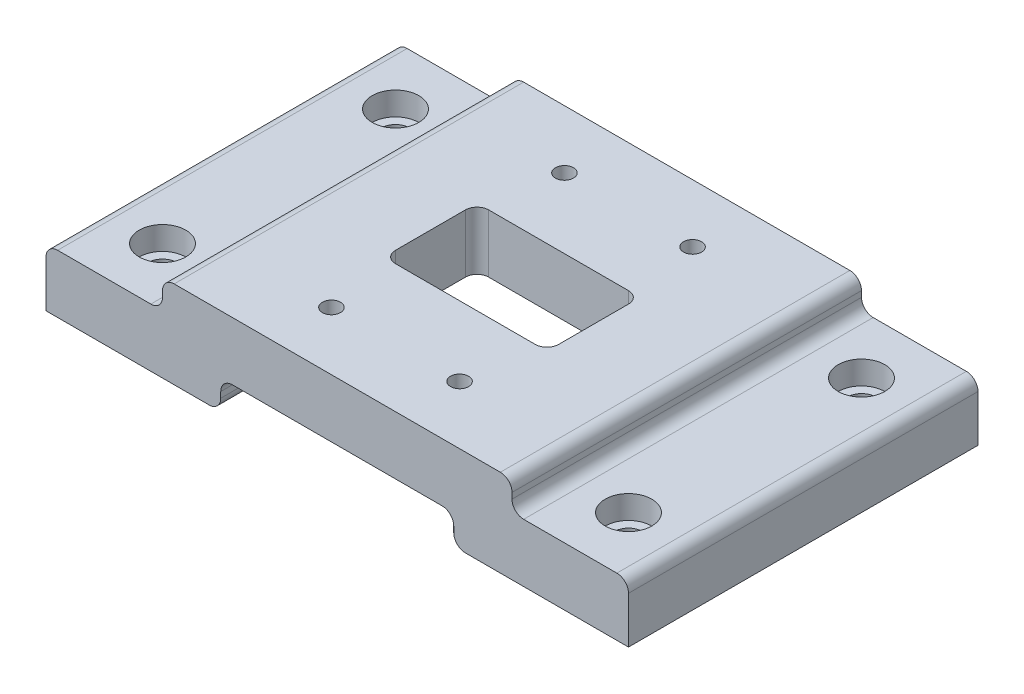
SolidWorks part; units mm, degrees
ref_plane "Front Plane" through (0, 0, 0) normal (0, 0, 1) x (1, 0, 0)
ref_plane "Top Plane" through (0, 0, 0) normal (0, 1, 0) x (1, 0, 0)
ref_plane "Right Plane" through (0, 0, 0) normal (1, 0, 0) x (0, 0, -1)
sketch "Sketch2" plane through (0, 0, 0) normal (0, 1, 0) x (1, 0, 0)
  line L0 (-30, 30) -> (30, 30)
  line L1 (-30, 30) -> (-30, -30)
  line L2 (30, 30) -> (30, -30)
  line L3 (-30, -30) -> (30, -30)
  line L4 (30, -30) -> (-30, 30) construction
  point P0 (0, 0)
  dimension "D1" = 60
  dimension "D2" = 60
extrude "Boss-Extrude1" add sketch "Sketch2" along normal blind 10
sketch "Sketch7" plane through (0, 10, 0) normal (0, 1, 0) x (1, 0, 0)
  line L0 (-14, 8) -> (14, 8)
  line L1 (-14, 8) -> (-14, -8)
  line L2 (14, 8) -> (14, -8)
  line L3 (-14, -8) -> (14, -8)
  line L4 (14, -8) -> (-14, 8) construction
  point P0 (0, 0)
  dimension "D1" = 28
  dimension "D2" = 16
extrude "Cut-Extrude2" cut sketch "Sketch7" against normal through all
fillet "Fillet2" radius 2 4 edges at (-14, 5, 8) (14, 5, 8) (14, 5, -8) (-14, 5, -8)
hole_wizard "CBORE for M2.5 SHCS2" positions "Sketch9" profile "Sketch10" counterbore size "M2.5" standard "ANSI Metric" end condition up to next
sketch "Sketch9" plane through (0, 0, 0) normal (0, -1, 0) x (-1, 0, 0)
  line L0 (-11, 20) -> (11, 20) construction
  line L1 (-11, 20) -> (-11, -20) construction
  line L2 (11, 20) -> (11, -20) construction
  line L3 (-11, -20) -> (11, -20) construction
  line L4 (11, -20) -> (-11, 20) construction
  point P0 (11, -20)
  point P2 (-11, -20)
  point P4 (11, 20)
  point P6 (-11, 20)
  point P50 (0, 0)
  dimension "D1" = 22
  dimension "D2" = 40
sketch "Sketch10" plane through (-11, 0, 20) normal (1, 0, 0) x (0, 0, -1)
  line L0 (0, 0) -> (0, 10)
  line L1 (0, 10) -> (1.55, 10)
  line L3 (1.55, 10) -> (1.55, 2.5)
  line L4 (1.55, 2.5) -> (2.75, 2.5)
  line L5 (2.75, 2.5) -> (2.75, 0)
  line L7 (2.75, 0) -> (0, 0)
  line L11 (0, -6.35) -> (0, 107.95) construction
  dimension "Thru Hole Dia." = 3.1
  dimension "Thru Hole Depth" = 10
  dimension "C'Bore Dia." = 5.5
  dimension "C'Bore Depth" = 2.5
other "Move Face1" face at (11, 2.5, 18.45) face at (-11, 2.5, 18.45) face at (11, 2.5, -21.55) face at (-11, 2.5, -21.55) parameters "D1"=3.5
sketch "Sketch11" plane through (0, 0, -30) normal (0, 0, -1) x (-1, 0, 0)
  line L0 (-30, 0) -> (-20, 0)
  line L1 (-30, 0) -> (-30, -5)
  line L2 (-20, 0) -> (-20, -5)
  line L3 (-30, -5) -> (-20, -5)
  line L4 (-30, 0) -> (30, 0) construction
  line L5 (-30, 10) -> (30, 10) construction
  dimension "D1" = 10
  dimension "D2" = 15
extrude "Boss-Extrude2" add sketch "Sketch11" against normal up to surface (60 mm away) up to face at (0, 5, 30)
sketch "Sketch12" plane through (0, -5, 0) normal (0, -1, 0) x (1, 0, 0)
  line L0 (30, 30) -> (30, -30)
  line L1 (30, 30) -> (50, 30)
  line L2 (30, -30) -> (50, -30)
  line L3 (50, 30) -> (50, -30)
  dimension "D1" = 20
extrude "Boss-Extrude3" add sketch "Sketch12" against normal blind 10
hole_wizard "CBORE for M4 SHCS1" positions "Sketch13" profile "Sketch14" counterbore size "M4" standard "ANSI Metric" end condition up to next
sketch "Sketch13" plane through (0, 5, 0) normal (0, 1, 0) x (1, 0, 0)
  line L4 (40, 0) -> (50, 0) construction
  line L5 (50, 30) -> (50, -30) construction
  line L7 (40, 20) -> (40, -20) construction
  line L9 (50, -30) -> (30, -30) construction
  point P0 (40, 20)
  point P2 (40, -20)
  point P24 (40, 0)
  point P28 (40, -30)
  dimension "D1" = 40
sketch "Sketch14" plane through (40, 5, -20) normal (1, 0, 0) x (0, 0, 1)
  line L0 (0, 0) -> (0, 10.001)
  line L1 (0, 10.001) -> (2.4, 10.001)
  line L3 (2.4, 10.001) -> (2.4, 4)
  line L4 (2.4, 4) -> (4, 4)
  line L5 (4, 4) -> (4, 0)
  line L7 (4, 0) -> (0, 0)
  line L11 (0, -6.35) -> (0, 107.95) construction
  dimension "Thru Hole Dia." = 4.8
  dimension "Thru Hole Depth" = 10.001
  dimension "C'Bore Dia." = 8
  dimension "C'Bore Depth" = 4
mirror "Mirror1" about plane through (0, 0, 0) normal (1, 0, 0) of "CBORE for M4 SHCS1", "Boss-Extrude3", "Boss-Extrude2"
fillet "Fillet5" radius 2 10 edges at (30, 10, 0) (-30, 10, 0) (-20, -5, 0) (20, -5, 0) (20, 0, 0) (-20, 0, 0) (30, 5, 0) (-30, 5, 0) (-50, 5, 0) (50, 5, 0)
